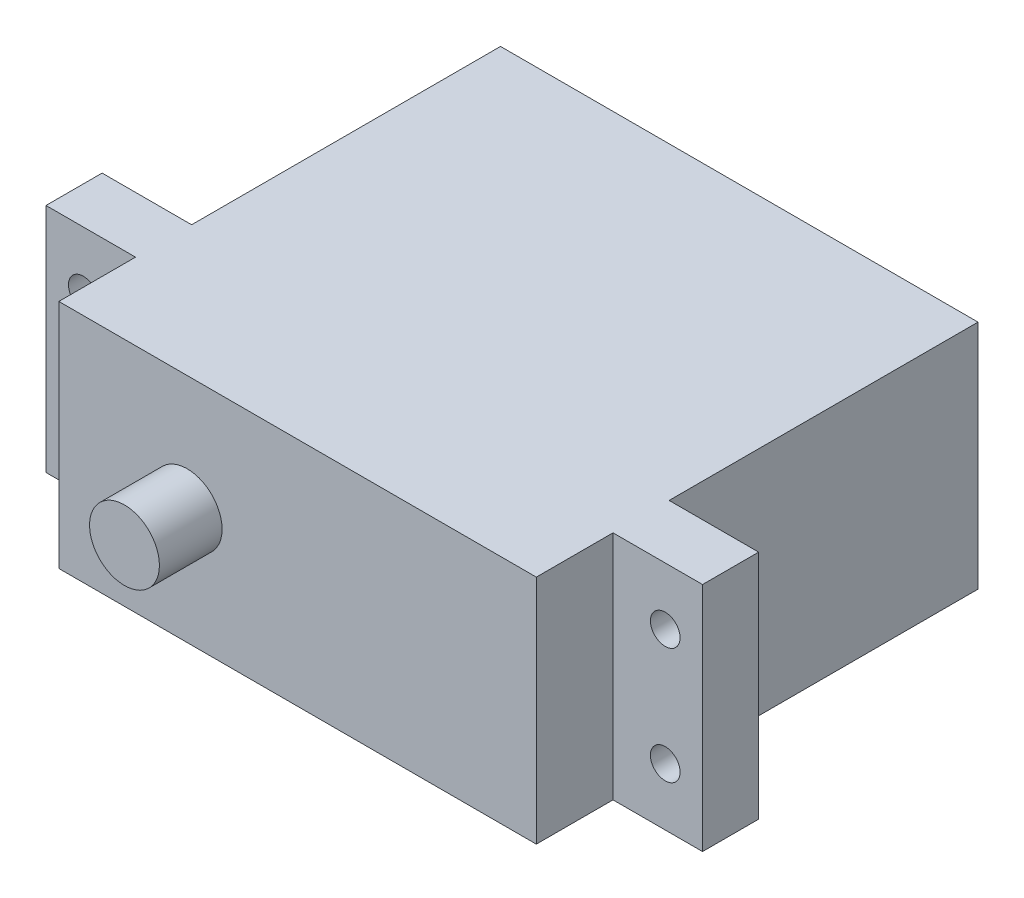
SolidWorks part; units mm, degrees
ref_plane "Front Plane" through (0, 0, 0) normal (0, 0, 1) x (1, 0, 0)
ref_plane "Top Plane" through (0, 0, 0) normal (0, 1, 0) x (1, 0, 0)
ref_plane "Right Plane" through (0, 0, 0) normal (1, 0, 0) x (0, 0, -1)
sketch "Sketch1" plane through (0, 0, 0) normal (0, 0, 1) x (1, 0, 0)
  line L0 (-27.94, -9.8425) -> (27.94, -9.8425)
  line L1 (-27.94, -9.8425) -> (-27.94, 9.8425)
  line L2 (27.94, -9.8425) -> (27.94, 9.8425)
  line L3 (-27.94, 9.8425) -> (27.94, 9.8425)
  line L4 (-27.94, -9.8425) -> (27.94, 9.8425) construction
  line L5 (27.94, -9.8425) -> (-27.94, 9.8425) construction
  point P1 (0, 0)
extrude "Extrude1" add sketch "Sketch1" along normal blind 42.926
sketch "Sketch3" plane through (0, 0, 42.926) normal (0, 0, 1) x (1, 0, 0)
  line L0 (-27.94, 0) -> (-9.398, 0) construction
  line L1 (-27.94, 9.8425) -> (-27.94, -9.8425) construction
  circle A0 centre (-9.398, 0) radius 2.9718
extrude "Extrude2" cut sketch "Sketch3" against normal blind 5.334 flip side to cut
sketch "Sketch11" plane through (0, 0, 37.592) normal (0, 0, 1) x (1, 0, 0)
  line L1 (-24.765, -4.953) -> (24.765, -4.953) construction
  line L2 (-24.765, -4.953) -> (-24.765, 4.953) construction
  line L3 (-24.765, 4.953) -> (24.765, 4.953) construction
  line L4 (24.765, -4.953) -> (24.765, 4.953) construction
  line L5 (-24.765, -4.953) -> (24.765, 4.953) construction
  line L6 (-24.765, 4.953) -> (24.765, -4.953) construction
  point P0 (0, 0)
sketch "Sketch8" plane through (0, 0, 0) normal (0, 0, -1) x (-1, 0, 0)
  line L0 (-27.94, -9.8425) -> (-27.94, 9.8425)
  line L2 (-27.94, 9.8425) -> (-20.32, 9.8425)
  line L4 (20.32, -9.8425) -> (20.32, 9.8425)
  line L5 (-27.94, 9.8425) -> (27.94, 9.8425) construction
  line L6 (-20.32, 9.8425) -> (-20.32, -9.8425)
  line L7 (27.94, -9.8425) -> (-27.94, -9.8425) construction
  line L8 (-20.32, -9.8425) -> (-27.94, -9.8425)
  line L9 (27.94, -9.8425) -> (20.32, -9.8425)
  line L10 (20.32, 9.8425) -> (27.94, 9.8425)
  line L11 (27.94, 9.8425) -> (27.94, -9.8425)
  point P10 (23.368, 0)
  point P11 (-23.368, 0)
extrude "Extrude5" cut sketch "Sketch8" against normal blind 26.289
hole_wizard "#39 (0.0995) Diameter Hole1" positions "3DSketch1" profile "Sketch12" hole size "#39" standard "Ansi Inch"
sketch3d "3DSketch1"
  point P0 (-24.765, 4.953, 37.592)
  point P3 (-24.765, -4.953, 37.592)
  point P6 (24.765, 4.953, 37.592)
  point P9 (24.765, -4.953, 37.592)
sketch "Sketch12" plane through (-24.765, 4.953, 37.592) normal (1, 0, 0) x (0, -1, 0)
  line L0 (0, 0) -> (0, 13.4593)
  line L1 (0, 13.4593) -> (1.2636, 12.7)
  line L2 (1.2636, 12.7) -> (1.2636, 0)
  line L5 (1.2636, 0) -> (0, 0)
  line L10 (0, 13.4593) -> (-1.2636, 12.7) construction
  line L11 (0, -6.35) -> (0, 107.95) construction
  dimension "Hole Dia." = 2.5273
  dimension "Hole Depth" = 12.7
  dimension "Drill Angle" = 118
sketch "Sketch13" plane through (0, 0, 37.592) normal (0, 0, 1) x (1, 0, 0)
  line L0 (-27.94, 9.8425) -> (-20.32, 9.8425)
  line L1 (27.94, 9.8425) -> (-27.94, 9.8425) construction
  line L2 (-20.32, 9.8425) -> (-20.32, -9.8425)
  line L3 (-27.94, -9.8425) -> (27.94, -9.8425) construction
  line L4 (-20.32, -9.8425) -> (-27.94, -9.8425)
  line L5 (-27.94, -9.8425) -> (-27.94, 9.8425)
  line L6 (27.94, 9.8425) -> (27.94, -9.8425)
  line L7 (27.94, -9.8425) -> (20.32, -9.8425)
  line L8 (20.32, -9.8425) -> (20.32, 9.8425)
  line L9 (20.32, 9.8425) -> (27.94, 9.8425)
extrude "Extrude6" cut sketch "Sketch13" against normal blind 6.5278
